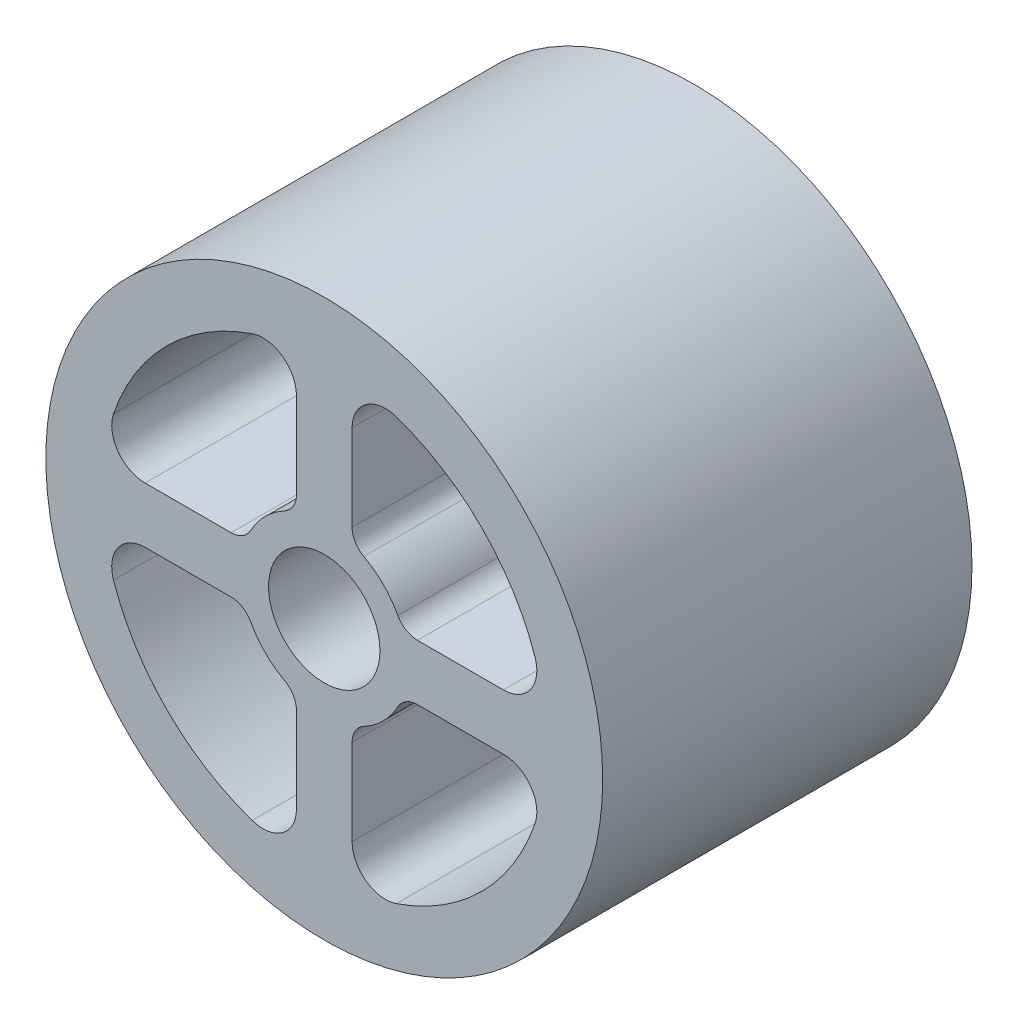
SolidWorks part; units mm, degrees
ref_plane "Ön Düzlem" through (0, 0, 0) normal (0, 0, 1) x (1, 0, 0)
ref_plane "Üst Düzlem" through (0, 0, 0) normal (0, 1, 0) x (1, 0, 0)
ref_plane "Sağ Düzlem" through (0, 0, 0) normal (1, 0, 0) x (0, 0, -1)
sketch "Çizim1" plane through (0, 0, 0) normal (0, 0, 1) x (1, 0, 0)
  line L0 (0, 63.5055) -> (0, -59.8514) construction
  line L1 (-69.3901, 0) -> (75.6211, 0) construction
  line L3 (30.5628, 4.75) -> (15.8965, 4.75)
  line L5 (4.75, 30.5628) -> (4.75, 15.8965)
  line L6 (-30.5628, 4.75) -> (-15.8965, 4.75)
  line L7 (-4.75, 30.5628) -> (-4.75, 15.8965)
  line L8 (4.75, -30.5628) -> (4.75, -15.8965)
  line L9 (30.5628, -4.75) -> (15.8965, -4.75)
  line L10 (-30.5628, -4.75) -> (-15.8965, -4.75)
  line L11 (-4.75, -30.5628) -> (-4.75, -15.8965)
  circle A0 centre (0, 0) radius 47.5
  circle A1 centre (0, 0) radius 9.5
  arc A7 (-12.2941, 35.9563) -> (-35.9563, 12.2941) centre (0, 0) ccw
  arc A8 (-6.75, 12.5499) -> (-12.5499, 6.75) centre (0, 0) ccw
  arc A9 (12.5499, 6.75) -> (6.75, 12.5499) centre (0, 0) ccw
  arc A10 (35.9563, 12.2941) -> (12.2941, 35.9563) centre (0, 0) ccw
  arc A11 (30.5628, 4.75) -> (35.9563, 12.2941) centre (30.5628, 10.45) ccw
  arc A12 (4.75, 30.5628) -> (12.2941, 35.9563) centre (10.45, 30.5628) cw
  arc A13 (4.75, 15.8965) -> (6.75, 12.5499) centre (8.55, 15.8965) ccw
  arc A14 (15.8965, 4.75) -> (12.5499, 6.75) centre (15.8965, 8.55) cw
  arc A15 (-30.5628, 4.75) -> (-35.9563, 12.2941) centre (-30.5628, 10.45) cw
  arc A16 (-15.8965, 4.75) -> (-12.5499, 6.75) centre (-15.8965, 8.55) ccw
  arc A17 (-4.75, 15.8965) -> (-6.75, 12.5499) centre (-8.55, 15.8965) cw
  arc A18 (-4.75, 30.5628) -> (-12.2941, 35.9563) centre (-10.45, 30.5628) ccw
  arc A19 (4.75, -30.5628) -> (12.2941, -35.9563) centre (10.45, -30.5628) ccw
  arc A20 (30.5628, -4.75) -> (35.9563, -12.2941) centre (30.5628, -10.45) cw
  arc A21 (4.75, -15.8965) -> (6.75, -12.5499) centre (8.55, -15.8965) cw
  arc A22 (15.8965, -4.75) -> (12.5499, -6.75) centre (15.8965, -8.55) ccw
  arc A23 (-4.75, -15.8965) -> (-6.75, -12.5499) centre (-8.55, -15.8965) ccw
  arc A24 (-15.8965, -4.75) -> (-12.5499, -6.75) centre (-15.8965, -8.55) cw
  arc A25 (-30.5628, -4.75) -> (-35.9563, -12.2941) centre (-30.5628, -10.45) ccw
  arc A26 (-4.75, -30.5628) -> (-12.2941, -35.9563) centre (-10.45, -30.5628) cw
  arc A27 (-12.5499, -6.75) -> (-6.75, -12.5499) centre (0, 0) ccw
  arc A28 (-35.9563, -12.2941) -> (-12.2941, -35.9563) centre (0, 0) ccw
  arc A29 (12.2941, -35.9563) -> (35.9563, -12.2941) centre (0, 0) ccw
  arc A30 (6.75, -12.5499) -> (12.5499, -6.75) centre (0, 0) ccw
  point P16 (0, 0)
  point P19 (37.702, 4.75)
  point P26 (13.435, 4.75)
  dimension "D1" = 95
  dimension "D2" = 19
  dimension "D6" = 4.75
  dimension "D3" = 76
  dimension "D4" = 28.5
  dimension "D5" = 4.75
  dimension "D7" = 5.7
  dimension "D8" = 3.8
extrude "Yükseklik-Ekstrüzyon1" add sketch "Çizim1" along normal blind 63
